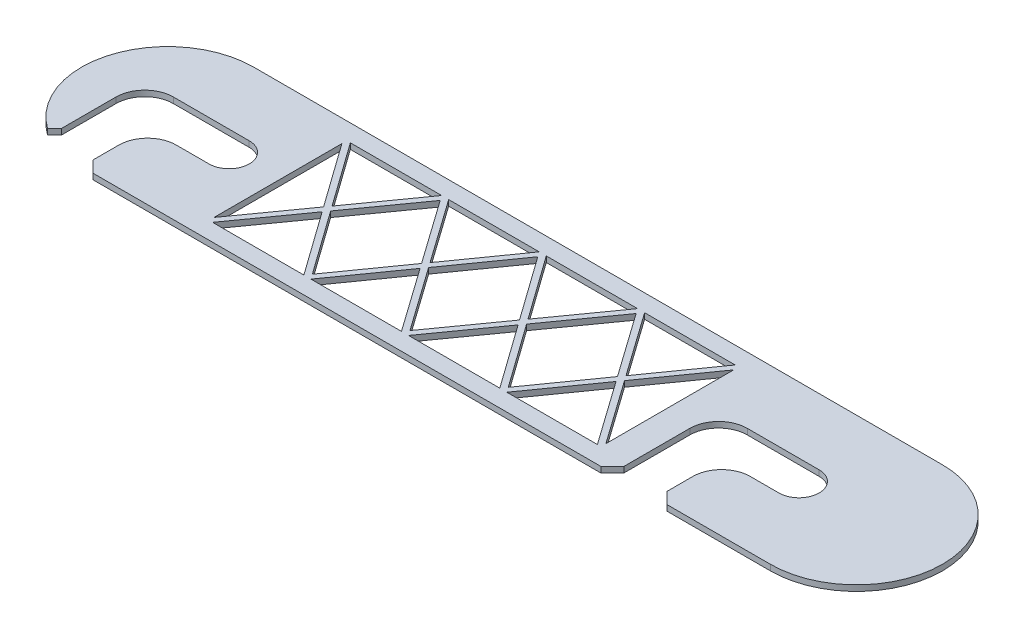
SolidWorks part; units mm, degrees
material "ABS"
ref_plane "Front Plane" through (0, 0, 0) normal (0, 0, 1) x (1, 0, 0)
ref_plane "Top Plane" through (0, 0, 0) normal (0, 1, 0) x (1, 0, 0)
ref_plane "Right Plane" through (0, 0, 0) normal (1, 0, 0) x (0, 0, -1)
sketch "Sketch1" plane through (0, 0, 0) normal (0, 1, 0) x (1, 0, 0)
  line L0 (-60, 0) -> (60, 0) construction
  line L1 (-60, 15) -> (60, 15)
  line L2 (-58, -15) -> (30.4798, -15)
  line L3 (-67.5, -10.9904) -> (-67.5, -1.5)
  line L4 (-62.5, 3.5) -> (-49.2848, 3.5)
  line L5 (-60, -13) -> (-60, -8.5)
  line L6 (-55, -3.5) -> (-49.2848, -3.5)
  line L7 (32.4798, -13) -> (32.4798, -1.5)
  line L8 (37.4798, 3.5) -> (50, 3.5)
  line L9 (40, -13) -> (40, -8.5)
  line L10 (45, -3.5) -> (50, -3.5)
  line L11 (-60, -13) -> (-58, -15)
  line L12 (-67.5, -10.9904) -> (-68.7169, -12.2072)
  line L13 (32.4798, -13) -> (30.4798, -15)
  line L14 (40, -13) -> (42, -15)
  line L15 (42, -15) -> (60, -15)
  arc A0 (-60, 15) -> (-68.7169, -12.2072) centre (-60, 0) ccw
  arc A1 (60, -15) -> (60, 15) centre (60, 0) ccw
  arc A2 (-49.2848, 3.5) -> (-49.2848, -3.5) centre (-49.2848, 0) cw
  arc A3 (50, 3.5) -> (50, -3.5) centre (50, 0) cw
  arc A4 (32.4798, -1.5) -> (37.4798, 3.5) centre (37.4798, -1.5) cw
  arc A5 (40, -8.5) -> (45, -3.5) centre (45, -8.5) cw
  arc A6 (-67.5, -1.5) -> (-62.5, 3.5) centre (-62.5, -1.5) cw
  arc A7 (-60, -8.5) -> (-55, -3.5) centre (-55, -8.5) cw
  point P3 (0, 0)
  point P9 (-60, -10.75)
  point P22 (-74.2848, 4.5767)
  point P23 (75, 0)
  dimension "D2" = 15
  dimension "D3" = 3.5
  dimension "D4" = 3.5
  dimension "D10" = 5
  dimension "D7" = 15
  dimension "D8" = 120
  dimension "D5" = 25
  dimension "D6" = 25
  dimension "D9" = 7.5
  dimension "D11" = 120
  dimension "D12" = 45
  dimension "D13" = 45
  dimension "D14" = 60
  dimension "D16" = 45
  dimension "D17" = 45
extrude "Boss-Extrude1" add sketch "Sketch1" along normal blind 2
sketch "Sketch2" plane through (0, 2, 0) normal (0, 1, 0) x (1, 0, 0)
  line L0 (-40.7848, -12) -> (-40.7848, 12)
  line L1 (-58, -15) -> (30.4798, -15) construction
  line L2 (60, 15) -> (-60, 15) construction
  line L3 (27.4798, 12) -> (27.4798, -12)
  line L4 (32.4798, -13) -> (32.4798, -1.5) construction
  line L5 (-40.7848, 12) -> (27.4798, 12)
  line L6 (-40.7848, -12) -> (27.4798, -12)
  arc A0 (-49.2848, -3.5) -> (-49.2848, 3.5) centre (-49.2848, 0) ccw construction
  point P9 (-45.7848, 0)
  dimension "D1" = 5
  dimension "D2" = 5
  dimension "D3" = 3
  dimension "D4" = 3
extrude "Cut-Extrude2" cut sketch "Sketch2" against normal blind 1.9
sketch "Sketch3" plane through (0, 2, 0) normal (0, 1, 0) x (1, 0, 0)
  line L1 (27.4798, 12) -> (-40.7848, 12) construction
  line L2 (-40.7848, -12) -> (27.4798, -12) construction
  line L3 (-6.6525, -12) -> (-23.6525, 12)
  line L4 (27.4798, 12) -> (-40.7848, 12) construction
  line L5 (-23.6525, 12) -> (-40.7848, -12)
  line L6 (-6.6525, -12) -> (10.4798, 12)
  line L7 (10.4798, 12) -> (27.4798, -12)
  line L8 (-6.6525, 0) -> (-13.7302, 0) construction
  line L9 (10.4798, -12) -> (27.4798, 12)
  line L10 (-6.6525, 12) -> (10.4798, -12)
  line L11 (-23.6525, -12) -> (-40.7848, 12)
  line L12 (-6.6525, 12) -> (-23.6525, -12)
  dimension "D1" = 17
rib "Rib1" sketch "Sketch3" sketch "Sketch3" thickness 1 extrusion direction normal to sketch draft on no parameters "D1"=1
sketch "Sketch4" plane through (0, 0, 0) normal (0, -1, 0) x (1, 0, 0)
  line L1 (-87.2769, 30.7085) -> (112.8289, 30.7085)
  line L2 (-87.2769, 30.7085) -> (-87.2769, -45.4856)
  line L3 (-87.2769, -45.4856) -> (112.8289, -45.4856)
  line L4 (112.8289, 30.7085) -> (112.8289, -45.4856)
extrude "Cut-Extrude3" cut sketch "Sketch4" against normal blind 1
